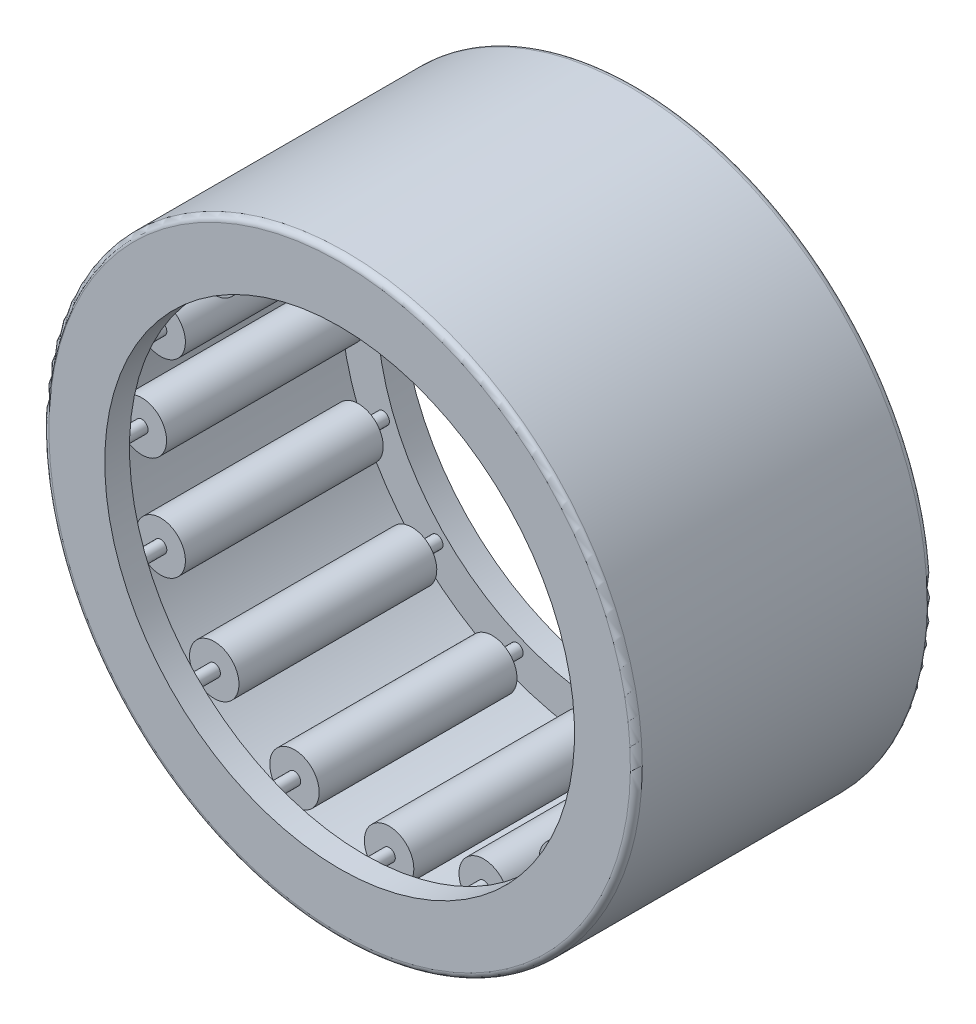
SolidWorks part; units mm, degrees
material "Cast Alloy Steel"
ref_plane "Front Plane" through (0, 0, 0) normal (0, 0, 1) x (1, 0, 0)
ref_plane "Top Plane" through (0, 0, 0) normal (0, 1, 0) x (1, 0, 0)
ref_plane "Right Plane" through (0, 0, 0) normal (1, 0, 0) x (0, 0, -1)
sketch "Sketch1" plane through (0, 0, 0) normal (1, 0, 0) x (0, 0, -1)
  line L0 (-6.35, 0) -> (6.35, 0) construction
  line L1 (0, 0) -> (0, 12.7) construction
  line L2 (-6.35, 0) -> (-6.35, 12.7) construction
  line L3 (-6.35, 12.7) -> (6.35, 12.7)
  line L4 (6.35, 12.7) -> (6.35, 0) construction
  line L5 (6.35, 0) -> (5.2917, 0) construction
  line L6 (5.2917, 0) -> (5.2917, 11.6417) construction
  line L7 (5.2917, 11.6417) -> (-5.2917, 11.6417)
  line L8 (-5.2917, 11.6417) -> (-5.2917, 0) construction
  line L9 (-5.2917, 0) -> (-6.35, 0) construction
  line L10 (-6.35, 12.7) -> (-6.35, 10.0542)
  line L11 (-6.35, 10.0542) -> (-5.2917, 10.0542)
  line L12 (-5.2917, 10.0542) -> (-5.2917, 11.6417)
  line L13 (5.2917, 12.7) -> (5.2917, 11.6417) construction
  line L14 (5.2917, 11.6417) -> (5.2917, 10.0542)
  line L15 (5.2917, 10.0542) -> (6.35, 10.0542)
  line L16 (6.35, 10.0542) -> (6.35, 12.7)
  line L17 (5.2917, 11.6417) -> (5.2917, 10.5833) construction
  line L18 (5.2917, 10.5833) -> (5.2917, 9.525) construction
  line L19 (5.2917, -11.6417) -> (5.2917, -10.5833) construction
  line L20 (5.2917, -12.7) -> (5.2917, -11.6417) construction
  line L21 (6.35, -10.0542) -> (6.35, -12.7) construction
  line L22 (5.2917, -10.0542) -> (6.35, -10.0542) construction
  line L23 (5.2917, -11.6417) -> (5.2917, -10.0542) construction
  line L24 (-5.2917, -10.0542) -> (-5.2917, -11.6417) construction
  line L25 (-6.35, -10.0542) -> (-5.2917, -10.0542) construction
  line L26 (-6.35, -12.7) -> (-6.35, -10.0542) construction
  line L27 (5.2917, -11.6417) -> (-5.2917, -11.6417) construction
  line L28 (-6.35, -12.7) -> (6.35, -12.7) construction
  point P5 (0, 9.525)
  dimension "Width" = 12.7
  dimension "OD" = 25.4
  dimension "Shaft Dia" = 19.05
revolve "Revolve1" add sketch "Sketch1" angle 360 about L0
sketch "Sketch2" plane through (0, 0, 0) normal (1, 0, 0) x (0, 0, -1)
  line L0 (5.2917, 11.6417) -> (-5.2917, 11.6417) construction
  line L1 (-4.2333, 10.5833) -> (4.2333, 10.5833) construction
  line L2 (-4.2333, 10.5833) -> (-4.2333, 11.6417) construction
  line L3 (-4.2333, 11.6417) -> (4.2333, 11.6417)
  line L4 (4.2333, 10.5833) -> (4.2333, 11.6417) construction
  line L5 (5.2917, 10.0542) -> (6.35, 10.0542) construction
  line L6 (-5.2917, 10.5833) -> (-4.2333, 10.5833) construction
  line L7 (4.2333, 10.5833) -> (5.2917, 10.5833) construction
  line L8 (-6.35, 10.0542) -> (-5.2917, 10.0542) construction
  line L9 (-4.2333, 10.8479) -> (-4.2333, 10.3188) construction
  line L10 (-5.2917, 10.5833) -> (-5.2917, 10.0542) construction
  line L11 (-4.2333, 11.6417) -> (-4.2333, 10.8479)
  line L12 (4.2333, 11.6417) -> (4.2333, 10.8479)
  line L13 (4.2333, 10.8479) -> (-4.2333, 10.8479)
  line L14 (0, 11.6417) -> (0, 9.525) construction
  line L15 (-5.2917, 10.0542) -> (-5.2917, 11.6417) construction
  line L16 (-4.2333, 10.3188) -> (-5.2917, 10.3188) construction
  line L17 (0, 0) -> (6.35, 0) construction
  line L18 (-4.2333, -10.3188) -> (-5.2917, -10.3188) construction
  line L19 (0, -11.6417) -> (0, -9.525) construction
  line L20 (-5.2917, -10.5833) -> (-5.2917, -10.0542) construction
  line L21 (-4.2333, -10.8479) -> (-4.2333, -10.3188) construction
  line L22 (4.2333, -10.5833) -> (5.2917, -10.5833) construction
  line L23 (-5.2917, -10.5833) -> (-4.2333, -10.5833) construction
  line L24 (4.2333, -10.5833) -> (4.2333, -11.6417) construction
  line L25 (-4.2333, -10.5833) -> (-4.2333, -11.6417) construction
  line L26 (-4.2333, -10.5833) -> (4.2333, -10.5833) construction
  line L27 (4.2333, -10.8479) -> (-4.2333, -10.8479) construction
  line L28 (4.2333, -11.6417) -> (4.2333, -10.8479) construction
  line L29 (-4.2333, -11.6417) -> (-4.2333, -10.8479) construction
  line L30 (-4.2333, -11.6417) -> (4.2333, -11.6417) construction
  line L31 (6.35, -12.7) -> (6.35, 12.7) construction
  point P16 (0, 10.5833)
revolve "Revolve2" add sketch "Sketch2" angle 360 about L1
sketch "Sketch3" plane through (0, 0, 0) normal (1, 0, 0) x (0, 0, -1)
  line L0 (5.2917, 11.6417) -> (5.2917, 10.0542) construction
  line L1 (-5.2917, 10.5833) -> (5.2917, 10.5833)
  line L2 (-5.2917, 10.5833) -> (-5.2917, 10.8479)
  line L3 (-5.2917, 10.8479) -> (5.2917, 10.8479)
  line L4 (5.2917, 10.5833) -> (5.2917, 10.8479)
  line L5 (0, 0) -> (6.35, 0) construction
  line L6 (6.35, -12.7) -> (6.35, 12.7) construction
  line L7 (5.2917, -10.5833) -> (5.2917, -10.8479) construction
  line L8 (-5.2917, -10.8479) -> (5.2917, -10.8479) construction
  line L9 (-5.2917, -10.5833) -> (-5.2917, -10.8479) construction
  line L10 (-5.2917, -10.5833) -> (5.2917, -10.5833) construction
revolve "Revolve3" add sketch "Sketch3" angle 360 about L1
ref_axis "Axis1" through (0, 0, -6.35) along (0, 0, 1)
pattern_circular "CirPattern1" count 16 every 22.5 about axis through (0, 0, -6.35) along (0, 0, 1) of bodies 166 167
fillet "Fillet1" radius 0.254 2 edges at (0, -12.7, -6.35) (0, -12.7, 6.35)
sketch "Sketch4" plane through (0, 0, 0) normal (1, 0, 0) x (0, 0, -1)
  line L1 (6.096, 9.525) -> (4.2333, 9.525)
  line L2 (6.096, 9.525) -> (6.096, 10.0542)
  line L3 (6.096, 10.0542) -> (4.2333, 10.0542)
  line L4 (4.2333, 9.525) -> (4.2333, 10.0542)
  line L5 (-6.35, 10.0542) -> (-5.2917, 10.0542) construction
  line L6 (6.096, -12.7) -> (6.096, 12.7) construction
  line L7 (4.2333, 11.6417) -> (4.2333, 10.8479) construction
revolve "Revolve4" [suppressed] add sketch "Sketch4" angle 360 about L0
sketch "Sketch5" plane through (0, 0, 0) normal (1, 0, 0) x (0, 0, -1)
  line L0 (-6.096, 12.7) -> (-6.096, -12.7) construction
  line L1 (-4.2333, 9.525) -> (-6.096, 9.525)
  line L2 (-4.2333, 9.525) -> (-4.2333, 10.0542)
  line L3 (-4.2333, 10.0542) -> (-6.096, 10.0542)
  line L4 (-6.096, 9.525) -> (-6.096, 10.0542)
  line L6 (-4.2333, 11.6417) -> (-4.2333, 10.8479) construction
  line L7 (-6.35, 10.0542) -> (-5.2917, 10.0542) construction
revolve "Revolve5" [suppressed] add sketch "Sketch5" angle 360 about L0
equation "\"Angle@CirPattern1\" = 360/\"Rollers@CirPattern1\""
equation "\"Rollers@CirPattern1\" = \"OD@Sketch1\"*16"
equation "\"D1@Fillet1\" = \"OD@Sketch1\"*.01"
